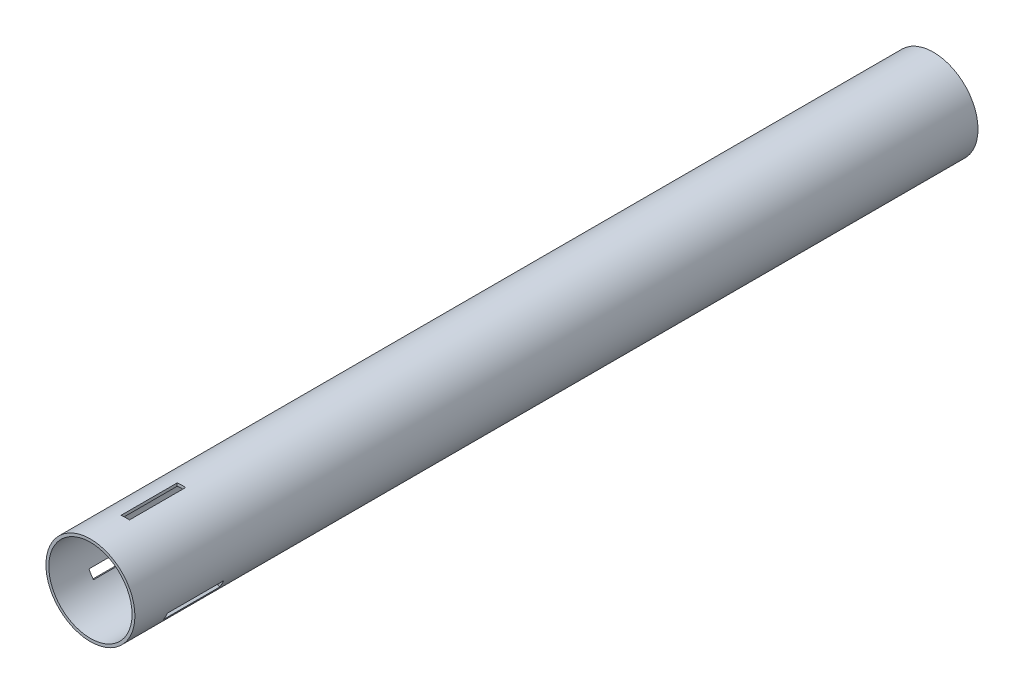
SolidWorks part; units mm, degrees
ref_plane "Front Plane" through (0, 0, 0) normal (0, 0, 1) x (1, 0, 0)
ref_plane "Top Plane" through (0, 0, 0) normal (0, 1, 0) x (1, 0, 0)
ref_plane "Right Plane" through (0, 0, 0) normal (1, 0, 0) x (0, 0, -1)
sketch "Sketch1" plane through (0, 0, 0) normal (0, 0, 1) x (1, 0, 0)
  circle A0 centre (0, 0) radius 23.75
  circle A1 centre (0, 0) radius 22.225
  dimension "D1" = 47.5
  dimension "D2" = 44.45
extrude "Boss-Extrude1" add sketch "Sketch1" along normal blind 450
ref_plane "Plane1" through (0, 100, 0) normal (0, 1, 0) x (1, 0, 0)
sketch "Sketch2" plane through (0, 100, 0) normal (0, 1, 0) x (1, 0, 0)
  line L3 (1.5875, -430.7565) -> (1.5875, -400.7565)
  line L4 (-2.9417, -430.7565) -> (-2.9417, -400.7565)
  line L5 (-2.9417, -400.7565) -> (1.5875, -400.7565)
  line L6 (-2.9417, -430.7565) -> (1.5875, -430.7565)
  dimension "D1" = 4.5292
  dimension "D2" = 30
extrude "Cut-Extrude1" cut sketch "Sketch2" against normal up to next
pattern_circular "CirPattern2" count 3 over 360 about axis through (0, 0, 0) along (0, 0, 1) of "Cut-Extrude1"
